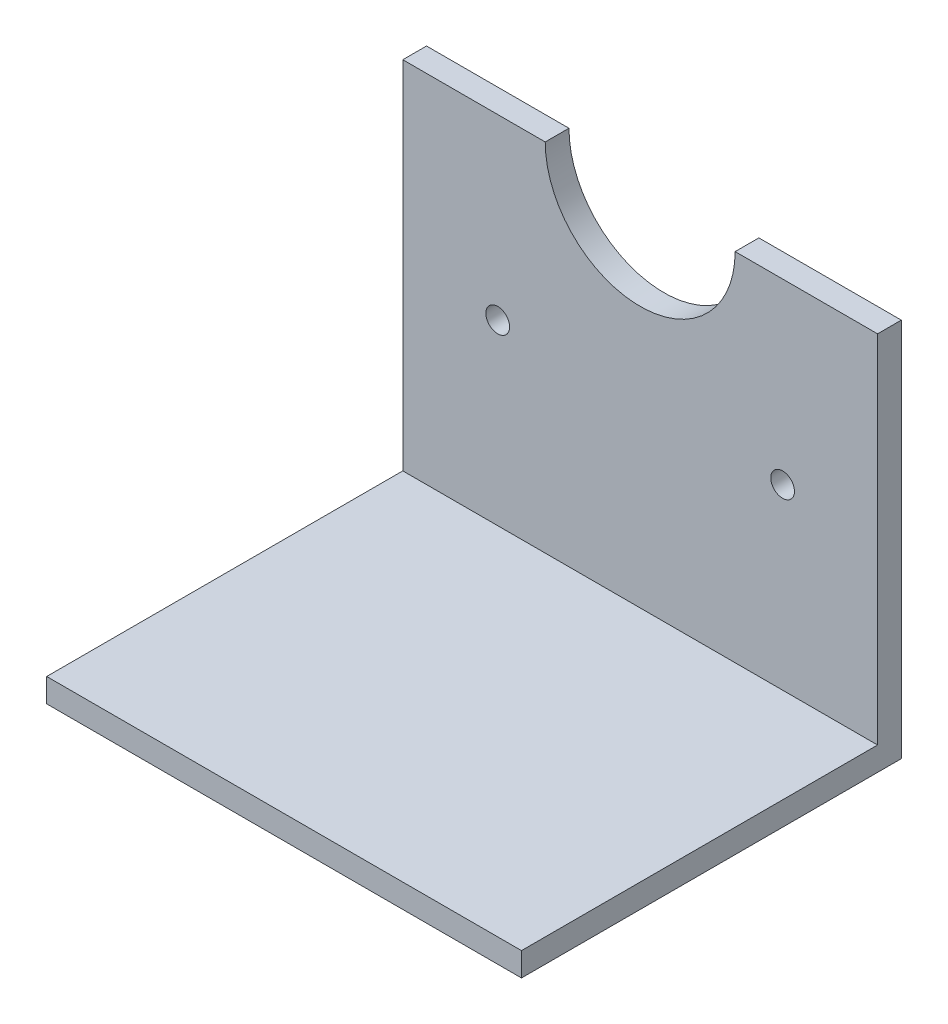
SolidWorks part; units mm, degrees
ref_plane "Front Plane" through (0, 0, 0) normal (0, 0, 1) x (1, 0, 0)
ref_plane "Top Plane" through (0, 0, 0) normal (0, 1, 0) x (1, 0, 0)
ref_plane "Right Plane" through (0, 0, 0) normal (1, 0, 0) x (0, 0, -1)
sketch "Sketch1" plane through (0, 0, 0) normal (1, 0, 0) x (0, 0, -1)
  line L1 (-3.175, 0) -> (-50.8, 0)
  line L2 (0, 0) -> (0, -3.175)
  line L3 (0, -3.175) -> (-50.8, -3.175)
  line L4 (-50.8, 0) -> (-50.8, -3.175)
  line L6 (0, 0) -> (0, 47.625)
  line L7 (0, 47.625) -> (-3.175, 47.625)
  line L8 (-3.175, 0) -> (-3.175, 47.625)
  dimension "D1" = 3.175
  dimension "D2" = 50.8
  dimension "D3" = 50.8
  dimension "D4" = 3.175
extrude "Boss-Extrude1" add sketch "Sketch1" along normal blind 63.5
sketch "Sketch2" plane through (0, 0, 3.175) normal (0, 0, 1) x (1, 0, 0)
  line L0 (12.7, 23.8125) -> (50.8, 23.8125) construction
  line L3 (31.75, 23.8125) -> (31.75, 47.625) construction
  line L4 (63.5, 47.625) -> (0, 47.625) construction
  circle A0 centre (31.75, 47.625) radius 12.7
  circle A1 centre (12.7, 23.8125) radius 1.5875
  circle A2 centre (50.8, 23.8125) radius 1.5875
  dimension "D1" = 25.4
  dimension "D2" = 3.175
  dimension "D3" = 38.1
extrude "Cut-Extrude1" cut sketch "Sketch2" against normal up to surface (3.175 mm away) up to face at (31.75, 22.225, 0)
